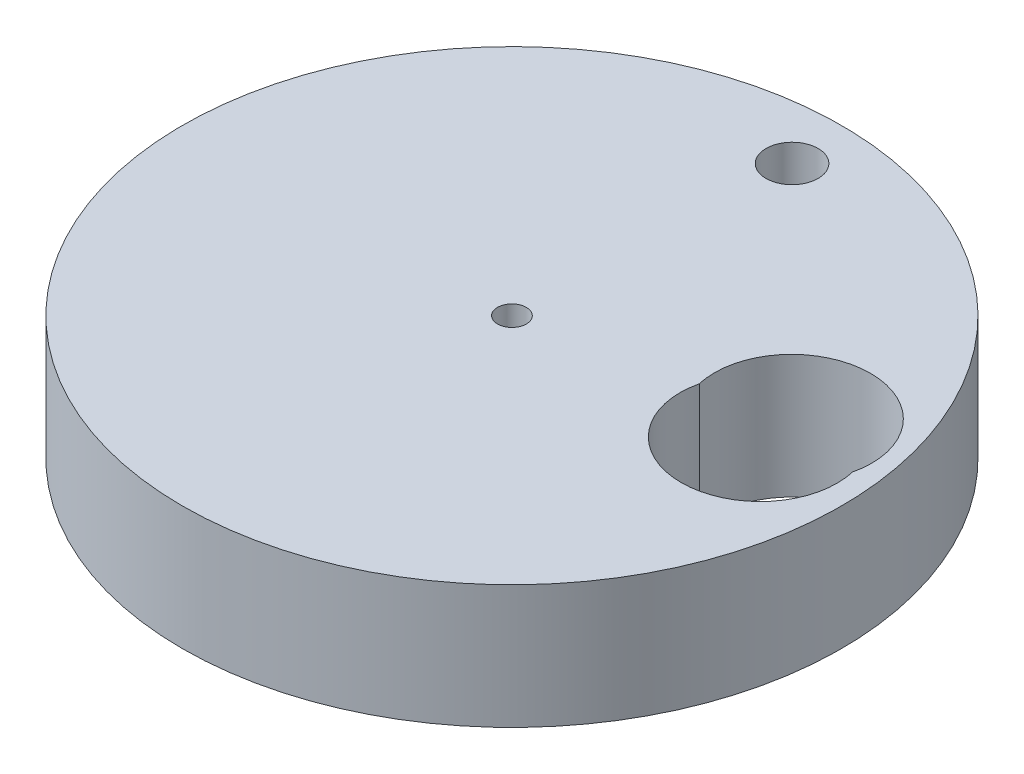
SolidWorks part; units mm, degrees
material "Polyurethane Foam Rigid"
ref_plane "Front Plane" through (0, 0, 0) normal (0, 0, 1) x (1, 0, 0)
ref_plane "Top Plane" through (0, 0, 0) normal (0, 1, 0) x (1, 0, 0)
ref_plane "Right Plane" through (0, 0, 0) normal (1, 0, 0) x (0, 0, -1)
sketch "Sketch1" plane through (0, 0, 0) normal (0, 1, 0) x (1, 0, 0)
  circle A0 centre (0, 0) radius 50.8
  circle A1 centre (1.27, 41.91) radius 4.0132 construction
  circle A2 centre (0, 0) radius 2.2225 construction
  circle A3 centre (1.27, 41.91) radius 4.0132
  circle A4 centre (0, 0) radius 2.2225
  ellipse E0 centre (35.325, 8.0287) end of major axis (47.425, 8.0287) minor radius 11.9162 construction
  ellipse E1 centre (35.325, 2.6804) end of major axis (47.425, 2.6804) minor radius 11.9162 (44.525, 10.4203) -> (44.525, -5.0596) ccw construction
  ellipse E2 centre (35.325, 8.0287) end of major axis (47.425, 8.0287) minor radius 11.9162
  ellipse E3 centre (35.325, 2.6804) end of major axis (47.425, 2.6804) minor radius 11.9162 (44.525, 10.4203) -> (44.525, -5.0596) ccw
  ellipse E4 centre (35.325, 2.6804) end of major axis (47.425, 2.6804) minor radius 11.9162 (44.525, -5.0596) -> (44.525, 10.4203) ccw construction
  ellipse E5 centre (35.325, 2.6804) end of major axis (47.425, 2.6804) minor radius 11.9162 (44.525, -5.0596) -> (44.525, 10.4203) ccw
  dimension "D1" = 101.6
extrude "Boss-Extrude1" add sketch "Sketch1" along normal blind 19.05 contours A0 E5 E3 E2 A4 A3
